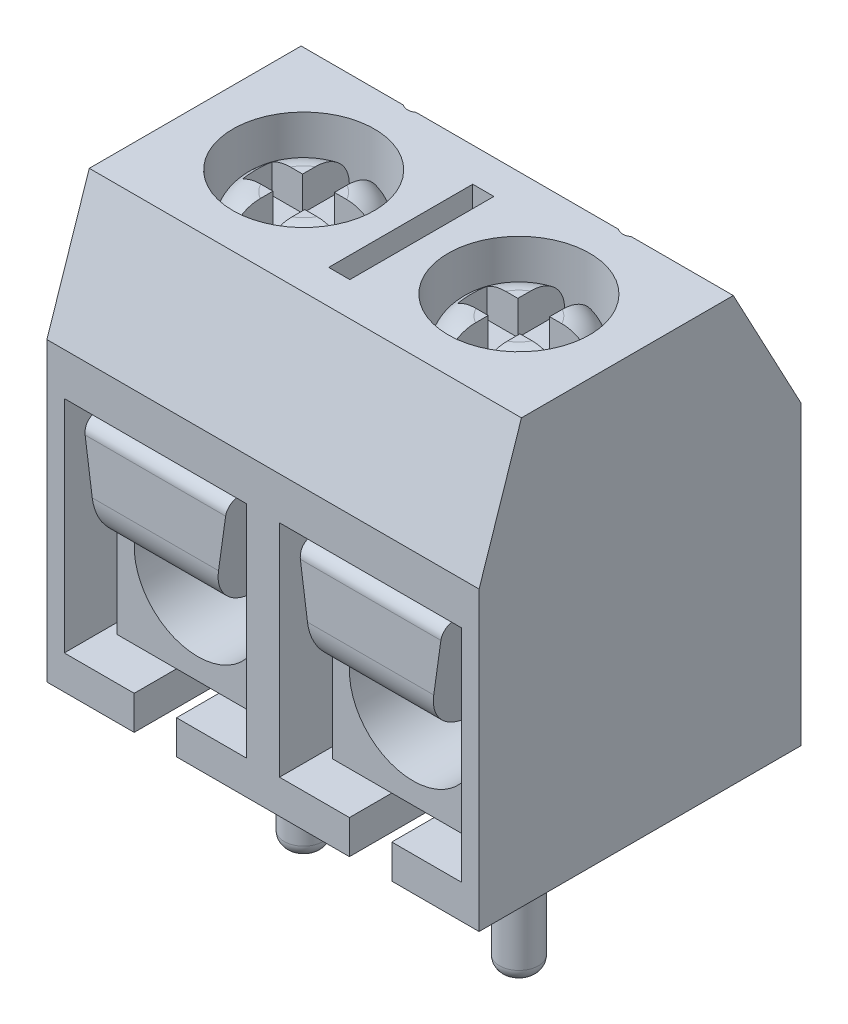
SolidWorks part; units mm, degrees
other "Plastic"
other "Metal"
ref_plane "Front Plane" through (0, 0, 0) normal (0, 0, 1) x (1, 0, 0)
ref_plane "Top Plane" through (0, 0, 0) normal (0, 1, 0) x (1, 0, 0)
ref_plane "Right Plane" through (0, 0, 0) normal (1, 0, 0) x (0, 0, -1)
sketch "Sketch1" plane through (0, 0, 0) normal (1, 0, 0) x (0, 0, -1)
  line L0 (-3.5, 0) -> (4.1, 0)
  line L1 (-3.5, 0) -> (-3.5, 7)
  line L2 (4.1, 0) -> (4.1, 7)
  line L3 (0, 0) -> (0, 10) construction
  line L4 (-2.5, 10) -> (2.5, 10)
  line L5 (4.1, 7) -> (2.5, 10)
  line L6 (-3.5, 7) -> (-2.5, 10)
  dimension "D1" = 3.5
  dimension "D2" = 7.6
  dimension "D3" = 5
  dimension "D4" = 10
  dimension "D5" = 7
extrude "Boss-Extrude1" add sketch "Sketch1" along normal mid plane 10.2
sketch "Sketch3" plane through (0, 10, 0) normal (0, 1, 0) x (1, 0, 0)
  line L0 (-2.54, 0) -> (2.54, 0) construction
  circle A1 centre (-2.54, 0) radius 1.67
  circle A2 centre (2.54, 0) radius 1.67
  dimension "D1" = 3.34
  dimension "D2" = 5.08
extrude "Cut-Extrude1" cut sketch "Sketch3" against normal blind 1.75
sketch "Sketch4" plane through (0, 10, 0) normal (0, 1, 0) x (1, 0, 0)
  line L0 (-2.54, 0) -> (2.54, 0) construction
  line L1 (-2.54, 0) -> (-2.54, 2.7) construction
  line L2 (2.54, 0) -> (2.54, 2.7) construction
  line L22 (-0.25, 1.7) -> (0.25, 1.7)
  line L23 (-0.25, 1.7) -> (-0.25, -1.7)
  line L24 (-0.25, -1.7) -> (0.25, -1.7)
  line L25 (0.25, 1.7) -> (0.25, -1.7)
  line L26 (-0.25, 1.7) -> (0.25, -1.7) construction
  line L27 (-0.25, -1.7) -> (0.25, 1.7) construction
  circle A9 centre (-2.54, 2.7) radius 0.25
  circle A10 centre (2.54, 2.7) radius 0.25
  point P37 (0, 0)
  dimension "D1" = 2.7
  dimension "D2" = 0.5
  dimension "D5" = 0.5
  dimension "D6" = 3.4
extrude "Cut-Extrude2" cut sketch "Sketch4" against normal blind 2
sketch "Sketch5" plane through (0, 0, 3.5) normal (0, 0, 1) x (1, 0, 0)
  line L0 (0, 0) -> (0, 0.8) construction
  line L1 (0, 6) -> (0, 10) construction
  line L6 (5.1, 10) -> (-5.1, 10) construction
  line L7 (-0.39, 0.8) -> (0.39, 0.8) construction
  line L8 (-5.08, 0) -> (5.08, 0) construction
  line L9 (-2.54, 0.8) -> (-2.54, 6) construction
  line L10 (2.54, 6) -> (2.54, 0.8) construction
  line L12 (-4.69, 6) -> (-0.39, 6)
  line L13 (-4.69, 6) -> (-4.69, 0.8)
  line L14 (-4.69, 0.8) -> (-0.39, 0.8)
  line L15 (-0.39, 6) -> (-0.39, 0.8)
  line L16 (0.39, 6) -> (4.69, 6)
  line L17 (0.39, 6) -> (0.39, 0.8)
  line L18 (0.39, 0.8) -> (4.69, 0.8)
  line L19 (4.69, 6) -> (4.69, 0.8)
  dimension "D4" = 10.16
  dimension "D1" = 4.3
  dimension "D2" = 4
  dimension "D3" = 0.8
  dimension "D5" = 5.08
  dimension "D6" = 5.2
extrude "Cut-Extrude3" cut sketch "Sketch5" against normal blind 6
sketch "Sketch6" plane through (0, 0, 0) normal (0, -1, 0) x (1, 0, 0)
  line L1 (5.1, 3.5) -> (-5.1, 3.5) construction
  line L6 (-2.54, 0) -> (2.54, 0) construction
  line L7 (-2.54, 0) -> (-2.54, 3.5) construction
  line L8 (-3.04, 0) -> (-3.04, 3.5)
  line L9 (-2.04, 0) -> (-2.04, 3.5)
  line L10 (2.54, 0) -> (2.54, 3.5) construction
  line L11 (2.04, 0) -> (2.04, 3.5)
  line L12 (3.04, 0) -> (3.04, 3.5)
  arc A2 (-3.04, 0) -> (-2.04, 0) centre (-2.54, 0) ccw
  arc A3 (-2.04, 3.5) -> (-3.04, 3.5) centre (-2.54, 3.5) ccw
  arc A4 (2.04, 0) -> (3.04, 0) centre (2.54, 0) ccw
  arc A5 (3.04, 3.5) -> (2.04, 3.5) centre (2.54, 3.5) ccw
  point P16 (-2.54, 1.75)
  point P22 (2.54, 1.75)
  dimension "D1" = 5.08
  dimension "D2" = 1
extrude "Cut-Extrude4" cut sketch "Sketch6" against normal up to surface (0.8 mm away) up to face at (-2.54, 0.8, 0.5)
sketch "Sketch9" plane through (0, 8.25, 0) normal (0, 1, 0) x (1, 0, 0)
  circle A1 centre (2.54, 0) radius 1.5
  circle A2 centre (-2.54, 0) radius 1.5
  dimension "D1" = 3
extrude "Boss-Extrude5" add sketch "Sketch9" along normal blind 1.3
fillet "Fillet1" radius 0.75 2 edges at (2.54, 9.55, 1.5) (-2.54, 9.55, 1.5)
sketch "Sketch10" plane through (0, 9.55, 0) normal (0, 1, 0) x (1, 0, 0)
  line L7 (-2.915, 1.55) -> (-2.165, 1.55)
  line L8 (-2.915, 1.55) -> (-2.915, -1.55)
  line L9 (-2.915, -1.55) -> (-2.165, -1.55)
  line L10 (-2.165, 1.55) -> (-2.165, -1.55)
  line L11 (-2.915, 1.55) -> (-2.165, -1.55) construction
  line L12 (-2.915, -1.55) -> (-2.165, 1.55) construction
  line L13 (2.165, 1.55) -> (2.915, 1.55)
  line L14 (2.165, 1.55) -> (2.165, -1.55)
  line L15 (2.165, -1.55) -> (2.915, -1.55)
  line L16 (2.915, 1.55) -> (2.915, -1.55)
  line L17 (2.165, 1.55) -> (2.915, -1.55) construction
  line L18 (2.165, -1.55) -> (2.915, 1.55) construction
  point P5 (-2.54, 0)
  point P11 (2.54, 0)
  dimension "D1" = 0.75
  dimension "D2" = 3.1
extrude "Cut-Extrude5" cut sketch "Sketch10" against normal blind 0.8
sketch "Sketch11" plane through (0, 9.55, 0) normal (0, 1, 0) x (1, 0, 0)
  line L0 (-2.54, 0) -> (0, 0) construction
  line L5 (0, 0) -> (2.54, 0) construction
  line L7 (-3.64, 0.35) -> (-1.44, 0.35)
  line L8 (-3.64, 0.35) -> (-3.64, -0.35)
  line L9 (-3.64, -0.35) -> (-1.44, -0.35)
  line L10 (-1.44, 0.35) -> (-1.44, -0.35)
  line L11 (-3.64, 0.35) -> (-1.44, -0.35) construction
  line L12 (-3.64, -0.35) -> (-1.44, 0.35) construction
  line L13 (1.44, 0.35) -> (3.64, 0.35)
  line L14 (1.44, 0.35) -> (1.44, -0.35)
  line L15 (1.44, -0.35) -> (3.64, -0.35)
  line L16 (3.64, 0.35) -> (3.64, -0.35)
  line L17 (1.44, 0.35) -> (3.64, -0.35) construction
  line L18 (1.44, -0.35) -> (3.64, 0.35) construction
  point P5 (-2.54, 0)
  point P11 (2.54, 0)
  dimension "D1" = 0.7
  dimension "D2" = 2.2
extrude "Cut-Extrude6" cut sketch "Sketch11" against normal up to surface (0.8 mm away) up to face at (-2.54, 8.75, 0)
sketch "Sketch7" plane through (0, 0, -2.5) normal (0, 0, 1) x (1, 0, 0)
  line L0 (-4.69, 6) -> (-4.69, 0.8) construction
  line L1 (-4.69, 6) -> (4.69, 6)
  line L2 (-4.69, 6) -> (-4.69, 0.8)
  line L3 (-4.69, 0.8) -> (4.69, 0.8)
  line L4 (4.69, 6) -> (4.69, 0.8)
  line L5 (-0.39, 6) -> (-4.69, 6) construction
  line L6 (-0.39, 6) -> (-4.69, 6) construction
extrude "Boss-Extrude3" add sketch "Sketch7" along normal blind 0.5 separate body
sketch "Sketch8" plane through (0, 0, -2) normal (0, 0, 1) x (1, 0, 0)
  line L0 (-2.54, 0) -> (2.54, 0) construction
  line L1 (-2.54, 0) -> (-2.54, 0.8) construction
  line L2 (-2.04, 0.8) -> (-3.04, 0.8) construction
  line L3 (2.54, 0) -> (2.54, 0.8) construction
  line L4 (3.04, 0.8) -> (2.04, 0.8) construction
  line L8 (-4.44, 5.8) -> (-0.64, 5.8)
  line L9 (-4.44, 5.8) -> (-4.44, 0.8)
  line L10 (-4.44, 0.8) -> (-0.64, 0.8)
  line L11 (-0.64, 5.8) -> (-0.64, 0.8)
  line L16 (0.64, 5.8) -> (4.44, 5.8)
  line L17 (0.64, 5.8) -> (0.64, 0.8)
  line L18 (0.64, 0.8) -> (4.44, 0.8)
  line L19 (4.44, 5.8) -> (4.44, 0.8)
  line L21 (-2.54, 0.8) -> (-2.54, 2.8) construction
  line L22 (-2.54, 2.8) -> (-2.54, 5.8) construction
  line L23 (2.54, 0.8) -> (2.54, 2.8) construction
  line L24 (2.54, 2.8) -> (2.54, 5.8) construction
  circle A0 centre (-2.54, 2.8) radius 1.5
  circle A2 centre (2.54, 2.8) radius 1.5
  dimension "D4" = 3
  dimension "D1" = 3.8
  dimension "D2" = 5
  dimension "D3" = 2
extrude "Boss-Extrude4" add sketch "Sketch8" along normal offset from surface (4.5 mm away) 1 up to face at (0, 2.22, 3.5)
fillet "Fillet2" radius 0.2 4 edges at (4.44, 5.8, 0.25) (0.64, 5.8, 0.25) (-0.64, 5.8, 0.25) (-4.44, 5.8, 0.25)
sketch "Sketch12" plane through (0, 0, 3.5) normal (0, 0, 1) x (1, 0, 0)
  line L7 (2.54, 2.8) -> (2.54, 3.3) construction
  line L8 (2.54, 3.3) -> (2.54, 5.8) construction
  line L9 (0.84, 5.8) -> (4.24, 5.8) construction
  line L10 (-2.54, 2.8) -> (-2.54, 3.3) construction
  line L11 (-2.54, 3.3) -> (-2.54, 5.8) construction
  line L12 (-4.24, 5.8) -> (-0.84, 5.8) construction
  line L13 (-4.24, 5.8) -> (-0.84, 5.8)
  line L14 (0.84, 5.8) -> (4.24, 5.8)
  line L15 (-3.89, 3.3) -> (-1.19, 3.3)
  line L16 (1.19, 3.3) -> (3.89, 3.3)
  line L17 (-3.89, 3.3) -> (-4.24, 5.8)
  line L18 (-1.19, 3.3) -> (-0.84, 5.8)
  line L19 (1.19, 3.3) -> (0.84, 5.8)
  line L20 (3.89, 3.3) -> (4.24, 5.8)
  dimension "D1" = 0.5
  dimension "D2" = 2.7
extrude "Boss-Extrude6" add sketch "Sketch12" against normal up to surface (5.5 mm away) up to face at (0, 3.9104, -2)
fillet "Fillet3" radius 1 2 edges at (2.54, 3.3, 3.5) (-2.54, 3.3, 3.5)
fillet "Fillet4" radius 0.3 2 edges at (2.54, 5.8, 3.5) (-2.54, 5.8, 3.5)
sketch "Sketch13" plane through (0, 0.8, 0) normal (0, -1, 0) x (1, 0, 0)
  circle A1 centre (2.54, 0) radius 0.46
  circle A2 centre (-2.54, 0) radius 0.46
  dimension "D1" = 0.92
extrude "Boss-Extrude7" add sketch "Sketch13" along normal offset from surface (4.6 mm away) 3.8 up to face at (0, 0, 0.9833) offset beyond the face yes
fillet "Fillet5" radius 0.3 2 edges at (-2.54, -3.8, 0.46) (2.54, -3.8, 0.46)
